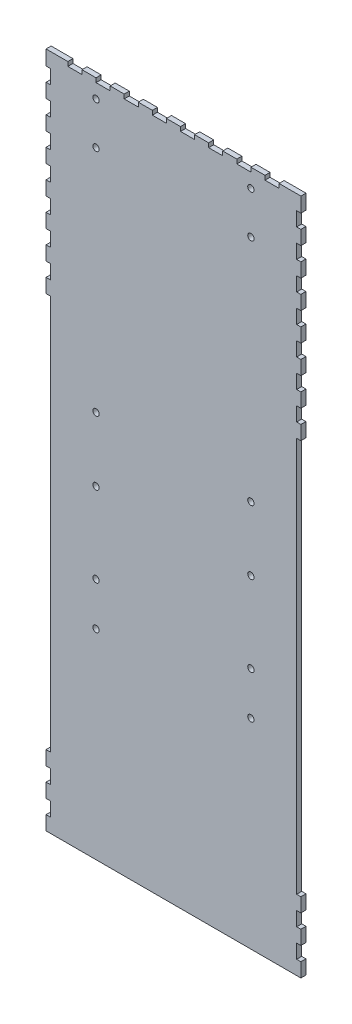
SolidWorks part; units mm, degrees
ref_plane "Front Plane" through (0, 0, 0) normal (0, 0, 1) x (1, 0, 0)
ref_plane "Top Plane" through (0, 0, 0) normal (0, 1, 0) x (1, 0, 0)
ref_plane "Right Plane" through (0, 0, 0) normal (1, 0, 0) x (0, 0, -1)
sketch "Sketch1" plane through (0, 0, 0) normal (0, 0, 1) x (1, 0, 0)
  line L2 (3, 408) -> (-12.5, 408)
  line L3 (-178, 408) -> (-178, 397.5)
  line L4 (-175, 0) -> (0, 0)
  line L5 (0, 0) -> (0, 405)
  line L6 (0, 405) -> (-175, 405)
  line L7 (-175, 405) -> (-175, 0)
  line L8 (-175, 0) -> (0, 0) construction
  line L10 (0, 405) -> (-175, 405) construction
  line L11 (-175, 405) -> (-175, 0) construction
  line L12 (-178, 397.5) -> (-175, 397.5)
  line L13 (-175, 397.5) -> (-175, 387.5)
  line L14 (-175, 387.5) -> (-178, 387.5)
  line L15 (-178, 387.5) -> (-178, 377.5)
  line L16 (-178, 408) -> (-178, -3) construction
  line L17 (-87.5, 408) -> (-87.5, -3) construction
  line L18 (-178, 377.5) -> (-175, 377.5)
  line L19 (-175, 377.5) -> (-175, 367.5)
  line L20 (-175, 367.5) -> (-178, 367.5)
  line L21 (-178, 357.5) -> (-175, 357.5)
  line L22 (-175, 357.5) -> (-175, 347.5)
  line L23 (-175, 347.5) -> (-178, 347.5)
  line L24 (-178, 337.5) -> (-175, 337.5)
  line L25 (-175, 337.5) -> (-175, 327.5)
  line L26 (-175, 327.5) -> (-178, 327.5)
  line L27 (-178, 317.5) -> (-175, 317.5)
  line L28 (-175, 317.5) -> (-175, 307.5)
  line L29 (-175, 307.5) -> (-178, 307.5)
  line L30 (-178, 297.5) -> (-175, 297.5)
  line L31 (-175, 297.5) -> (-175, 287.5)
  line L32 (-175, 287.5) -> (-178, 287.5)
  line L33 (-178, 277.5) -> (-175, 277.5)
  line L34 (-175, 277.5) -> (-175, 267.5)
  line L35 (-175, 267.5) -> (-178, 267.5)
  line L75 (-178, 367.5) -> (-178, 357.5)
  line L76 (-178, 347.5) -> (-178, 337.5)
  line L77 (-178, 327.5) -> (-178, 317.5)
  line L78 (-178, 307.5) -> (-178, 297.5)
  line L79 (-178, 287.5) -> (-178, 277.5)
  line L94 (3, -3) -> (3, 408) construction
  line L95 (0, 0) -> (0, 405) construction
  line L96 (0, 405) -> (0, 0) construction
  line L111 (3, 287.5) -> (3, 277.5)
  line L112 (3, 307.5) -> (3, 297.5)
  line L113 (3, 327.5) -> (3, 317.5)
  line L114 (3, 347.5) -> (3, 337.5)
  line L115 (3, 367.5) -> (3, 357.5)
  line L155 (0, 267.5) -> (3, 267.5)
  line L156 (0, 277.5) -> (0, 267.5)
  line L157 (3, 277.5) -> (0, 277.5)
  line L158 (0, 287.5) -> (3, 287.5)
  line L159 (0, 297.5) -> (0, 287.5)
  line L160 (3, 297.5) -> (0, 297.5)
  line L161 (0, 307.5) -> (3, 307.5)
  line L162 (0, 317.5) -> (0, 307.5)
  line L163 (3, 317.5) -> (0, 317.5)
  line L164 (0, 327.5) -> (3, 327.5)
  line L165 (0, 337.5) -> (0, 327.5)
  line L166 (3, 337.5) -> (0, 337.5)
  line L167 (0, 347.5) -> (3, 347.5)
  line L168 (0, 357.5) -> (0, 347.5)
  line L169 (3, 357.5) -> (0, 357.5)
  line L170 (0, 367.5) -> (3, 367.5)
  line L171 (0, 377.5) -> (0, 367.5)
  line L172 (3, 377.5) -> (0, 377.5)
  line L173 (3, 387.5) -> (3, 377.5)
  line L174 (0, 387.5) -> (3, 387.5)
  line L175 (0, 397.5) -> (0, 387.5)
  line L176 (3, 397.5) -> (0, 397.5)
  line L177 (3, 408) -> (3, 397.5)
  line L178 (-162.5, 408) -> (-162.5, 405)
  line L179 (-162.5, 405) -> (-152.5, 405)
  line L180 (-152.5, 405) -> (-152.5, 408)
  line L181 (-162.5, 408) -> (-178, 408)
  line L182 (3, 408) -> (-178, 408) construction
  line L183 (-142.5, 408) -> (-142.5, 405)
  line L184 (-132.5, 405) -> (-132.5, 408)
  line L185 (-142.5, 405) -> (-132.5, 405)
  line L186 (-122.5, 408) -> (-122.5, 405)
  line L187 (-112.5, 405) -> (-112.5, 408)
  line L188 (-122.5, 405) -> (-112.5, 405)
  line L189 (-102.5, 408) -> (-102.5, 405)
  line L190 (-92.5, 405) -> (-92.5, 408)
  line L191 (-102.5, 405) -> (-92.5, 405)
  line L192 (-82.5, 408) -> (-82.5, 405)
  line L193 (-72.5, 405) -> (-72.5, 408)
  line L194 (-82.5, 405) -> (-72.5, 405)
  line L195 (-62.5, 408) -> (-62.5, 405)
  line L196 (-52.5, 405) -> (-52.5, 408)
  line L197 (-62.5, 405) -> (-52.5, 405)
  line L198 (-42.5, 408) -> (-42.5, 405)
  line L199 (-32.5, 405) -> (-32.5, 408)
  line L200 (-42.5, 405) -> (-32.5, 405)
  line L201 (-22.5, 408) -> (-22.5, 405)
  line L202 (-12.5, 405) -> (-12.5, 408)
  line L203 (-22.5, 405) -> (-12.5, 405)
  line L204 (-142.5, 408) -> (-152.5, 408)
  line L205 (-122.5, 408) -> (-132.5, 408)
  line L206 (-102.5, 408) -> (-112.5, 408)
  line L207 (-82.5, 408) -> (-92.5, 408)
  line L208 (-62.5, 408) -> (-72.5, 408)
  line L209 (-42.5, 408) -> (-52.5, 408)
  line L210 (-22.5, 408) -> (-32.5, 408)
  line L211 (-178, 262.5) -> (-192.1885, 262.5) construction
  line L213 (-175, 247.5) -> (-178, 247.5) [skipped]
  line L214 (-178, 237.5) -> (-175, 237.5) [skipped]
  line L215 (-175, 237.5) -> (-175, 227.5) [skipped]
  line L216 (-175, 227.5) -> (-178, 227.5) [skipped]
  line L217 (-178, 217.5) -> (-175, 217.5) [skipped]
  line L218 (-175, 217.5) -> (-175, 207.5) [skipped]
  line L219 (-175, 207.5) -> (-178, 207.5) [skipped]
  line L220 (-178, 197.5) -> (-175, 197.5) [skipped]
  line L221 (-175, 197.5) -> (-175, 187.5) [skipped]
  line L222 (-175, 187.5) -> (-178, 187.5) [skipped]
  line L223 (-178, 177.5) -> (-175, 177.5) [skipped]
  line L224 (-175, 177.5) -> (-175, 167.5) [skipped]
  line L225 (-175, 167.5) -> (-178, 167.5) [skipped]
  line L226 (-178, 157.5) -> (-175, 157.5) [skipped]
  line L227 (-175, 157.5) -> (-175, 147.5) [skipped]
  line L228 (-175, 147.5) -> (-178, 147.5) [skipped]
  line L229 (-178, 137.5) -> (-175, 137.5) [skipped]
  line L230 (-175, 137.5) -> (-175, 127.5) [skipped]
  line L231 (-175, 127.5) -> (-178, 127.5) [skipped]
  line L232 (-178, 117.5) -> (-175, 117.5) [skipped]
  line L233 (-175, 117.5) -> (-175, 107.5) [skipped]
  line L234 (-175, 107.5) -> (-178, 107.5) [skipped]
  line L235 (-178, 97.5) -> (-175, 97.5) [skipped]
  line L236 (-175, 97.5) -> (-175, 87.5) [skipped]
  line L237 (-175, 87.5) -> (-178, 87.5) [skipped]
  line L238 (-178, 77.5) -> (-175, 77.5) [skipped]
  line L239 (-175, 77.5) -> (-175, 67.5) [skipped]
  line L240 (-175, 67.5) -> (-178, 67.5) [skipped]
  line L241 (-178, 57.5) -> (-175, 57.5) [skipped]
  line L242 (-175, 57.5) -> (-175, 47.5) [skipped]
  line L243 (-175, 47.5) -> (-178, 47.5) [skipped]
  line L244 (-178, 37.5) -> (-175, 37.5) [skipped]
  line L245 (-175, 37.5) -> (-175, 27.5) [skipped]
  line L246 (-175, 27.5) -> (-178, 27.5) [skipped]
  line L247 (-178, 17.5) -> (-175, 17.5) [skipped]
  line L248 (-175, 17.5) -> (-175, 7.5) [skipped]
  line L249 (-175, 7.5) -> (-178, 7.5) [skipped]
  line L250 (-175, 257.5) -> (-175, 247.5) [skipped]
  line L251 (-178, 257.5) -> (-175, 257.5) [skipped]
  line L254 (-178, -73) -> (3, -73)
  line L256 (-178, -3) -> (3, -3) construction
  line L257 (-178, -3) -> (3, -3) construction
  line L258 (-178, 267.5) -> (-178, 257.5)
  line L259 (-178, 257.5) -> (-175, 257.5)
  line L260 (3, 267.5) -> (3, 257.5)
  line L261 (3, 257.5) -> (0, 257.5)
  line L262 (-175, 257.5) -> (-175, 0)
  line L267 (0, 0) -> (0, 257.5)
  line L269 (-178, -23) -> (-175, -23)
  line L270 (-175, -23) -> (-175, 0)
  line L272 (3, -23) -> (0, -23)
  line L273 (0, -23) -> (0, 0)
  line L274 (-178, -33) -> (-175, -33)
  line L275 (-175, -33) -> (-175, -43)
  line L276 (-175, -43) -> (-178, -43)
  line L277 (-178, -43) -> (-178, -53)
  line L278 (-178, -53) -> (-175, -53)
  line L279 (-175, -53) -> (-175, -63)
  line L280 (-175, -63) -> (-178, -63)
  line L281 (-178, -33) -> (-178, -23)
  line L282 (-178, -73) -> (-178, -63)
  line L283 (3, -33) -> (0, -33)
  line L284 (0, -33) -> (0, -43)
  line L285 (0, -43) -> (3, -43)
  line L286 (3, -43) -> (3, -53)
  line L287 (3, -53) -> (0, -53)
  line L288 (0, -53) -> (0, -63)
  line L289 (0, -63) -> (3, -63)
  line L290 (3, -33) -> (3, -23)
  line L291 (3, -73) -> (3, -63)
  dimension "D3" = 10.5
  dimension "D4" = 10
  dimension "D6" = 10
  dimension "D7" = 10
  dimension "D8" = 15.5
  dimension "D10" = 10
  dimension "D11" = 481
  dimension "D12" = 10
  dimension "D13" = 50
  dimension "D14" = 50
  dimension "D15" = 3
  dimension "D16" = 3
  dimension "D17" = 3
  dimension "D18" = 10
  dimension "D19" = 10
  dimension "D20" = 10
  dimension "D21" = 10
  dimension "D22" = 10
  dimension "D23" = 10
  dimension "D24" = 10
  dimension "D25" = 10
  dimension "D26" = 10
  dimension "D27" = 10
  dimension "D28" = 10
  dimension "D1" = 0
  dimension "D2" = 3
  dimension "D5" = 20
  dimension "D9" = 8
extrude "Boss-Extrude1" add sketch "Sketch1" along normal blind 3.6
sketch "Sketch2" plane through (0, 0, 3.6) normal (0, 0, 1) x (1, 0, 0)
  line L116 (-175, 257.5) -> (-175, -23)
  line L117 (-175, -23) -> (-178, -23)
  line L118 (-178, -23) -> (-178, -33)
  line L119 (-178, -33) -> (-175, -33)
  line L120 (-175, -33) -> (-175, -43)
  line L121 (-175, -43) -> (-178, -43)
  line L122 (-178, -43) -> (-178, -53)
  line L123 (-178, -53) -> (-175, -53)
  line L124 (-175, -53) -> (-175, -63)
  line L125 (-175, -63) -> (-178, -63)
  line L126 (-178, -63) -> (-178, -73)
  line L127 (-178, -73) -> (3, -73)
  line L128 (3, -73) -> (3, -63)
  line L129 (3, -63) -> (0, -63)
  line L130 (0, -63) -> (0, -53)
  line L131 (0, -53) -> (3, -53)
  line L132 (3, -53) -> (3, -43)
  line L133 (3, -43) -> (0, -43)
  line L134 (0, -43) -> (0, -33)
  line L135 (0, -33) -> (3, -33)
  line L136 (3, -33) -> (3, -23)
  line L137 (3, -23) -> (0, -23)
  line L138 (0, -23) -> (0, 257.5)
  line L139 (0, 257.5) -> (3, 257.5)
  line L140 (3, 257.5) -> (3, 267.5)
  line L141 (3, 267.5) -> (0, 267.5)
  line L142 (0, 267.5) -> (0, 277.5)
  line L143 (0, 277.5) -> (3, 277.5)
  line L144 (3, 277.5) -> (3, 287.5)
  line L145 (3, 287.5) -> (0, 287.5)
  line L146 (0, 287.5) -> (0, 297.5)
  line L147 (0, 297.5) -> (3, 297.5)
  line L148 (3, 297.5) -> (3, 307.5)
  line L149 (3, 307.5) -> (0, 307.5)
  line L150 (0, 307.5) -> (0, 317.5)
  line L151 (0, 317.5) -> (3, 317.5)
  line L152 (3, 317.5) -> (3, 327.5)
  line L153 (3, 327.5) -> (0, 327.5)
  line L154 (0, 327.5) -> (0, 337.5)
  line L155 (0, 337.5) -> (3, 337.5)
  line L156 (3, 337.5) -> (3, 347.5)
  line L157 (3, 347.5) -> (0, 347.5)
  line L158 (0, 347.5) -> (0, 357.5)
  line L159 (0, 357.5) -> (3, 357.5)
  line L160 (3, 357.5) -> (3, 367.5)
  line L161 (3, 367.5) -> (0, 367.5)
  line L162 (0, 367.5) -> (0, 377.5)
  line L163 (0, 377.5) -> (3, 377.5)
  line L164 (3, 377.5) -> (3, 387.5)
  line L165 (3, 387.5) -> (0, 387.5)
  line L166 (0, 387.5) -> (0, 397.5)
  line L167 (0, 397.5) -> (3, 397.5)
  line L168 (3, 397.5) -> (3, 408)
  line L169 (3, 408) -> (-12.5, 408)
  line L170 (-12.5, 408) -> (-12.5, 405)
  line L171 (-12.5, 405) -> (-22.5, 405)
  line L172 (-22.5, 405) -> (-22.5, 408)
  line L173 (-22.5, 408) -> (-32.5, 408)
  line L174 (-32.5, 408) -> (-32.5, 405)
  line L175 (-32.5, 405) -> (-42.5, 405)
  line L176 (-42.5, 405) -> (-42.5, 408)
  line L177 (-42.5, 408) -> (-52.5, 408)
  line L178 (-52.5, 408) -> (-52.5, 405)
  line L179 (-52.5, 405) -> (-62.5, 405)
  line L180 (-62.5, 405) -> (-62.5, 408)
  line L181 (-62.5, 408) -> (-72.5, 408)
  line L182 (-72.5, 408) -> (-72.5, 405)
  line L183 (-72.5, 405) -> (-82.5, 405)
  line L184 (-82.5, 405) -> (-82.5, 408)
  line L185 (-82.5, 408) -> (-92.5, 408)
  line L186 (-92.5, 408) -> (-92.5, 405)
  line L187 (-92.5, 405) -> (-102.5, 405)
  line L188 (-102.5, 405) -> (-102.5, 408)
  line L189 (-102.5, 408) -> (-112.5, 408)
  line L190 (-112.5, 408) -> (-112.5, 405)
  line L191 (-112.5, 405) -> (-122.5, 405)
  line L192 (-122.5, 405) -> (-122.5, 408)
  line L193 (-122.5, 408) -> (-132.5, 408)
  line L194 (-132.5, 408) -> (-132.5, 405)
  line L195 (-132.5, 405) -> (-142.5, 405)
  line L196 (-142.5, 405) -> (-142.5, 408)
  line L197 (-142.5, 408) -> (-152.5, 408)
  line L198 (-152.5, 408) -> (-152.5, 405)
  line L199 (-152.5, 405) -> (-162.5, 405)
  line L200 (-162.5, 405) -> (-162.5, 408)
  line L201 (-162.5, 408) -> (-178, 408)
  line L202 (-178, 408) -> (-178, 397.5)
  line L203 (-178, 397.5) -> (-175, 397.5)
  line L204 (-175, 397.5) -> (-175, 387.5)
  line L205 (-175, 387.5) -> (-178, 387.5)
  line L206 (-178, 387.5) -> (-178, 377.5)
  line L207 (-178, 377.5) -> (-175, 377.5)
  line L208 (-175, 377.5) -> (-175, 367.5)
  line L209 (-175, 367.5) -> (-178, 367.5)
  line L210 (-178, 367.5) -> (-178, 357.5)
  line L211 (-178, 357.5) -> (-175, 357.5)
  line L212 (-175, 357.5) -> (-175, 347.5)
  line L213 (-175, 347.5) -> (-178, 347.5)
  line L214 (-178, 347.5) -> (-178, 337.5)
  line L215 (-178, 337.5) -> (-175, 337.5)
  line L216 (-175, 337.5) -> (-175, 327.5)
  line L217 (-175, 327.5) -> (-178, 327.5)
  line L218 (-178, 327.5) -> (-178, 317.5)
  line L219 (-178, 317.5) -> (-175, 317.5)
  line L220 (-175, 317.5) -> (-175, 307.5)
  line L221 (-175, 307.5) -> (-178, 307.5)
  line L222 (-178, 307.5) -> (-178, 297.5)
  line L223 (-178, 297.5) -> (-175, 297.5)
  line L224 (-175, 297.5) -> (-175, 287.5)
  line L225 (-175, 287.5) -> (-178, 287.5)
  line L226 (-178, 287.5) -> (-178, 277.5)
  line L227 (-178, 277.5) -> (-175, 277.5)
  line L228 (-175, 277.5) -> (-175, 267.5)
  line L229 (-175, 267.5) -> (-178, 267.5)
  line L230 (-178, 267.5) -> (-178, 257.5)
  line L231 (-178, 257.5) -> (-175, 257.5)
  line L232 (-175, 257.5) -> (-175, -23)
  line L233 (-175, -23) -> (-178, -23)
  line L234 (-178, -23) -> (-178, -33)
  line L235 (-178, -33) -> (-175, -33)
  line L236 (-175, -33) -> (-175, -43)
  line L237 (-175, -43) -> (-178, -43)
  line L238 (-178, -43) -> (-178, -53)
  line L239 (-178, -53) -> (-175, -53)
  line L240 (-175, -53) -> (-175, -63)
  line L241 (-175, -63) -> (-178, -63)
  line L242 (-178, -63) -> (-178, -73)
  line L243 (-178, -73) -> (3, -73)
  line L244 (3, -73) -> (3, -63)
  line L245 (3, -63) -> (0, -63)
  line L246 (0, -63) -> (0, -53)
  line L247 (0, -53) -> (3, -53)
  line L248 (3, -53) -> (3, -43)
  line L249 (3, -43) -> (0, -43)
  line L250 (0, -43) -> (0, -33)
  line L251 (0, -33) -> (3, -33)
  line L252 (3, -33) -> (3, -23)
  line L253 (3, -23) -> (0, -23)
  line L254 (0, -23) -> (0, 257.5)
  line L255 (0, 257.5) -> (3, 257.5)
  line L256 (3, 257.5) -> (3, 267.5)
  line L257 (3, 267.5) -> (0, 267.5)
  line L258 (0, 267.5) -> (0, 277.5)
  line L259 (0, 277.5) -> (3, 277.5)
  line L260 (3, 277.5) -> (3, 287.5)
  line L261 (3, 287.5) -> (0, 287.5)
  line L262 (0, 287.5) -> (0, 297.5)
  line L263 (0, 297.5) -> (3, 297.5)
  line L264 (3, 297.5) -> (3, 307.5)
  line L265 (3, 307.5) -> (0, 307.5)
  line L266 (0, 307.5) -> (0, 317.5)
  line L267 (0, 317.5) -> (3, 317.5)
  line L268 (3, 317.5) -> (3, 327.5)
  line L269 (3, 327.5) -> (0, 327.5)
  line L270 (0, 327.5) -> (0, 337.5)
  line L271 (0, 337.5) -> (3, 337.5)
  line L272 (3, 337.5) -> (3, 347.5)
  line L273 (3, 347.5) -> (0, 347.5)
  line L274 (0, 347.5) -> (0, 357.5)
  line L275 (0, 357.5) -> (3, 357.5)
  line L276 (3, 357.5) -> (3, 367.5)
  line L277 (3, 367.5) -> (0, 367.5)
  line L278 (0, 367.5) -> (0, 377.5)
  line L279 (0, 377.5) -> (3, 377.5)
  line L280 (3, 377.5) -> (3, 387.5)
  line L281 (3, 387.5) -> (0, 387.5)
  line L282 (0, 387.5) -> (0, 397.5)
  line L283 (0, 397.5) -> (3, 397.5)
  line L284 (3, 397.5) -> (3, 408)
  line L285 (3, 408) -> (-12.5, 408)
  line L286 (-12.5, 408) -> (-12.5, 405)
  line L287 (-12.5, 405) -> (-22.5, 405)
  line L288 (-22.5, 405) -> (-22.5, 408)
  line L289 (-22.5, 408) -> (-32.5, 408)
  line L290 (-32.5, 408) -> (-32.5, 405)
  line L291 (-32.5, 405) -> (-42.5, 405)
  line L292 (-42.5, 405) -> (-42.5, 408)
  line L293 (-42.5, 408) -> (-52.5, 408)
  line L294 (-52.5, 408) -> (-52.5, 405)
  line L295 (-52.5, 405) -> (-62.5, 405)
  line L296 (-62.5, 405) -> (-62.5, 408)
  line L297 (-62.5, 408) -> (-72.5, 408)
  line L298 (-72.5, 408) -> (-72.5, 405)
  line L299 (-72.5, 405) -> (-82.5, 405)
  line L300 (-82.5, 405) -> (-82.5, 408)
  line L301 (-82.5, 408) -> (-92.5, 408)
  line L302 (-92.5, 408) -> (-92.5, 405)
  line L303 (-92.5, 405) -> (-102.5, 405)
  line L304 (-102.5, 405) -> (-102.5, 408)
  line L305 (-102.5, 408) -> (-112.5, 408)
  line L306 (-112.5, 408) -> (-112.5, 405)
  line L307 (-112.5, 405) -> (-122.5, 405)
  line L308 (-122.5, 405) -> (-122.5, 408)
  line L309 (-122.5, 408) -> (-132.5, 408)
  line L310 (-132.5, 408) -> (-132.5, 405)
  line L311 (-132.5, 405) -> (-142.5, 405)
  line L312 (-142.5, 405) -> (-142.5, 408)
  line L313 (-142.5, 408) -> (-152.5, 408)
  line L314 (-152.5, 408) -> (-152.5, 405)
  line L315 (-152.5, 405) -> (-162.5, 405)
  line L316 (-162.5, 405) -> (-162.5, 408)
  line L317 (-162.5, 408) -> (-178, 408)
  line L318 (-178, 408) -> (-178, 397.5)
  line L319 (-178, 397.5) -> (-175, 397.5)
  line L320 (-175, 397.5) -> (-175, 387.5)
  line L321 (-175, 387.5) -> (-178, 387.5)
  line L322 (-178, 387.5) -> (-178, 377.5)
  line L323 (-178, 377.5) -> (-175, 377.5)
  line L324 (-175, 377.5) -> (-175, 367.5)
  line L325 (-175, 367.5) -> (-178, 367.5)
  line L326 (-178, 367.5) -> (-178, 357.5)
  line L327 (-178, 357.5) -> (-175, 357.5)
  line L328 (-175, 357.5) -> (-175, 347.5)
  line L329 (-175, 347.5) -> (-178, 347.5)
  line L330 (-178, 347.5) -> (-178, 337.5)
  line L331 (-178, 337.5) -> (-175, 337.5)
  line L332 (-175, 337.5) -> (-175, 327.5)
  line L333 (-175, 327.5) -> (-178, 327.5)
  line L334 (-178, 327.5) -> (-178, 317.5)
  line L335 (-178, 317.5) -> (-175, 317.5)
  line L336 (-175, 317.5) -> (-175, 307.5)
  line L337 (-175, 307.5) -> (-178, 307.5)
  line L338 (-178, 307.5) -> (-178, 297.5)
  line L339 (-178, 297.5) -> (-175, 297.5)
  line L340 (-175, 297.5) -> (-175, 287.5)
  line L341 (-175, 287.5) -> (-178, 287.5)
  line L342 (-178, 287.5) -> (-178, 277.5)
  line L343 (-178, 277.5) -> (-175, 277.5)
  line L344 (-175, 277.5) -> (-175, 267.5)
  line L345 (-175, 267.5) -> (-178, 267.5)
  line L346 (-178, 267.5) -> (-178, 257.5)
  line L347 (-178, 257.5) -> (-175, 257.5)
  dimension "D1" = 0
sketch "Sketch3" plane through (0, 0, 3.6) normal (0, 0, 1) x (1, 0, 0)
  circle A0 centre (-142.5, 365) radius 2.25 construction
  circle A1 centre (-142.5, 365) radius 2.25
  circle A2 centre (-32.5, 69.0494) radius 2.25 construction
  circle A3 centre (-32.5, 99.5494) radius 2.25 construction
  circle A4 centre (-142.5, 69.0494) radius 2.25 construction
  circle A5 centre (-142.5, 99.5494) radius 2.25 construction
  circle A6 centre (-142.5, 156.7198) radius 2.25 construction
  circle A7 centre (-32.5, 156.7198) radius 2.25 construction
  circle A8 centre (-32.5, 202.2198) radius 2.25 construction
  circle A9 centre (-142.5, 202.2198) radius 2.25 construction
  circle A10 centre (-32.5, 365) radius 2.25 construction
  circle A11 centre (-32.5, 395) radius 2.25 construction
  circle A12 centre (-142.5, 395) radius 2.25 construction
  circle A13 centre (-32.5, 69.0494) radius 2.25
  circle A14 centre (-32.5, 99.5494) radius 2.25
  circle A15 centre (-142.5, 69.0494) radius 2.25
  circle A16 centre (-142.5, 99.5494) radius 2.25
  circle A17 centre (-142.5, 156.7198) radius 2.25
  circle A18 centre (-32.5, 156.7198) radius 2.25
  circle A19 centre (-32.5, 202.2198) radius 2.25
  circle A20 centre (-142.5, 202.2198) radius 2.25
  circle A21 centre (-32.5, 365) radius 2.25
  circle A22 centre (-32.5, 395) radius 2.25
  circle A23 centre (-142.5, 395) radius 2.25
extrude "Cut-Extrude1" cut sketch "Sketch3" against normal blind 10
